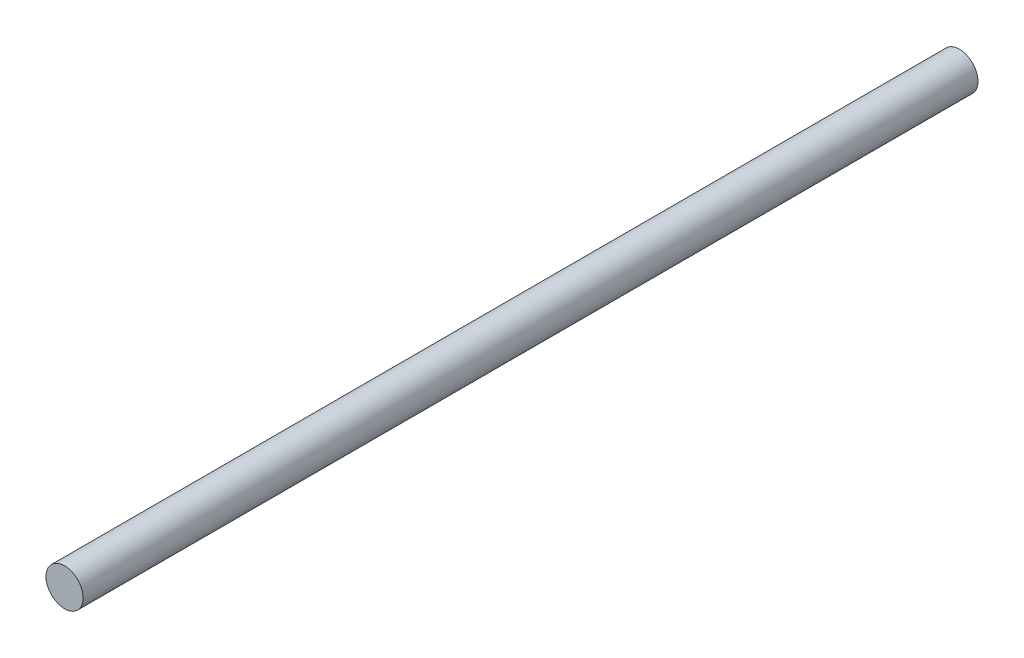
SolidWorks part; units mm, degrees
ref_plane "Front Plane" through (0, 0, 0) normal (0, 0, 1) x (1, 0, 0)
ref_plane "Top Plane" through (0, 0, 0) normal (0, 1, 0) x (1, 0, 0)
ref_plane "Right Plane" through (0, 0, 0) normal (1, 0, 0) x (0, 0, -1)
sketch "Sketch1" plane through (0, 0, 0) normal (0, 0, 1) x (1, 0, 0)
  circle A0 centre (0, 0) radius 6
  dimension "D1" = 12
extrude "Boss-Extrude1" add sketch "Sketch1" along normal blind 288.5
